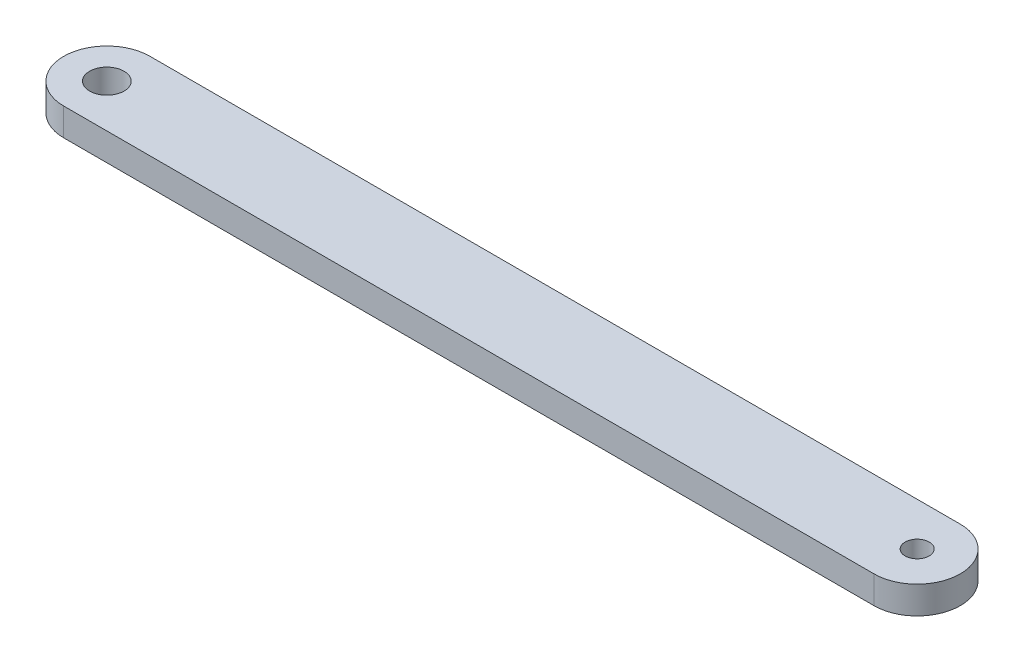
SolidWorks part; units mm, degrees
ref_plane "前视基准面" through (0, 0, 0) normal (0, 0, 1) x (1, 0, 0)
ref_plane "上视基准面" through (0, 0, 0) normal (0, 1, 0) x (1, 0, 0)
ref_plane "右视基准面" through (0, 0, 0) normal (1, 0, 0) x (0, 0, -1)
other "Configuration Table"
sketch "草图1" plane through (0, 0, 0) normal (0, 1, 0) x (1, 0, 0)
  line L0 (0, 0) -> (47, 0) construction
  line L1 (0, 2.5) -> (47, 2.5)
  line L2 (0, -2.5) -> (47, -2.5)
  arc A0 (0, 2.5) -> (0, -2.5) centre (0, 0) ccw
  arc A1 (47, -2.5) -> (47, 2.5) centre (47, 0) ccw
  circle A2 centre (0, 0) radius 1
  circle A3 centre (47, 0) radius 0.7
  point P3 (23.5, 0)
  dimension "D2" = 1.4
  dimension "D3" = 2
  dimension "D1" = 47
  dimension "D4" = 5
extrude "凸台-拉伸1" add sketch "草图1" along normal blind 1.6
